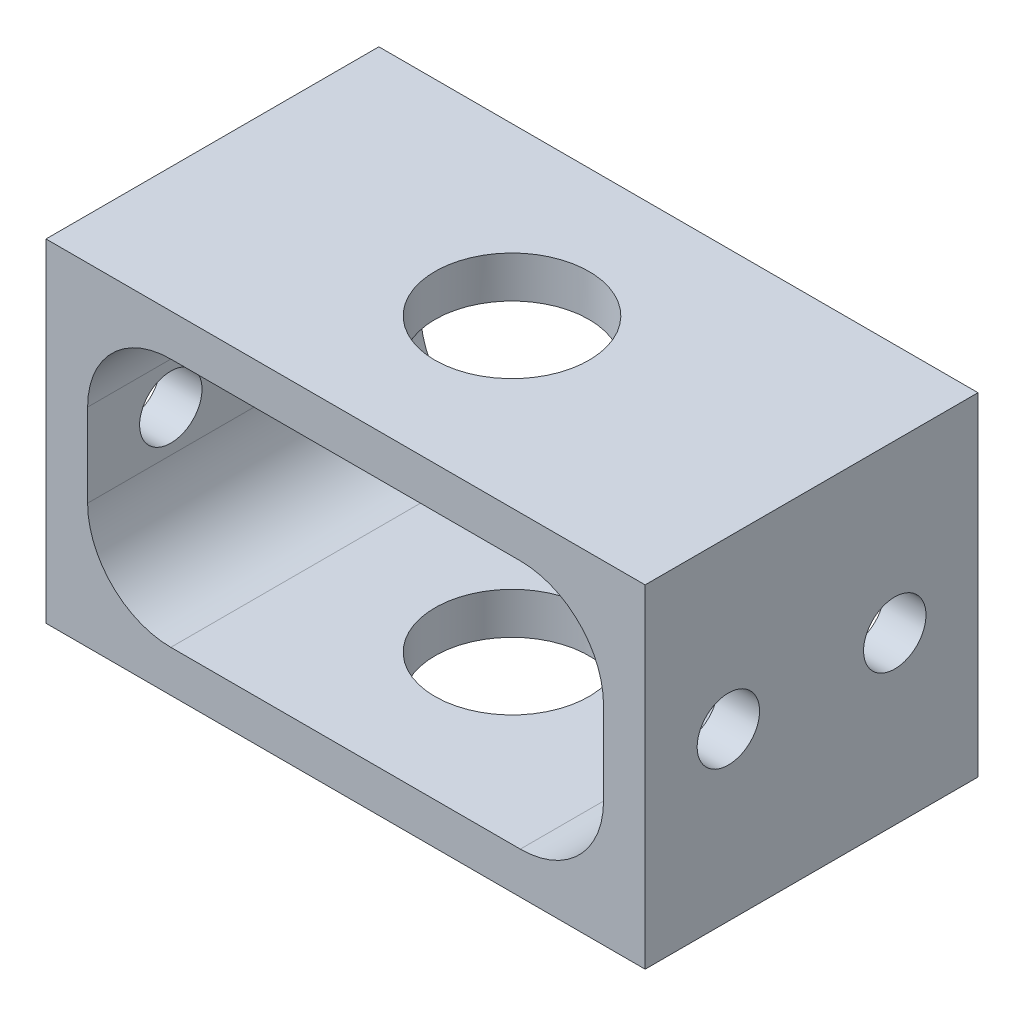
SolidWorks part; units mm, degrees
ref_plane "前视基准面" through (0, 0, 0) normal (0, 0, 1) x (1, 0, 0)
ref_plane "上视基准面" through (0, 0, 0) normal (0, 1, 0) x (1, 0, 0)
ref_plane "右视基准面" through (0, 0, 0) normal (1, 0, 0) x (0, 0, -1)
sketch "草图1" plane through (0, 0, 0) normal (0, 0, 1) x (1, 0, 0)
  line L9 (-14.4, 8) -> (-14.4, -8)
  line L10 (-12.4, 6) -> (12.4, 6)
  line L11 (-12.4, 6) -> (-12.4, -6)
  line L12 (-12.4, -6) -> (12.4, -6)
  line L13 (12.4, 6) -> (12.4, -6)
  line L14 (-12.4, 6) -> (12.4, -6) construction
  line L15 (-12.4, -6) -> (12.4, 6) construction
  line L16 (-14.4, -8) -> (14.4, -8)
  line L17 (14.4, 8) -> (14.4, -8)
  line L18 (-14.4, 8) -> (14.4, 8)
  point P0 (0, 0)
  dimension "D2" = 28.8
  dimension "D3" = 16
  dimension "D1" = 2
extrude "凸台-拉伸1" add sketch "草图1" along normal blind 16
sketch "草图2" plane through (14.4, 0, 0) normal (1, 0, 0) x (0, 0, -1)
  line L0 (-16, -8) -> (-16, 8) construction
  line L1 (0, -8) -> (0, 8) construction
  circle A0 centre (-12, 0) radius 1.5
  circle A1 centre (-4, 0) radius 1.5
  dimension "D1" = 3
  dimension "D2" = 4
  dimension "D3" = 4
extrude "切除-拉伸1" cut sketch "草图2" against normal up to surface (28.8 mm away) up to face at (-14.4, 0, 8)
sketch "草图3" plane through (0, 8, 0) normal (0, 1, 0) x (1, 0, 0)
  circle A0 centre (0, -8) radius 3.7
  dimension "D1" = 7.4
extrude "切除-拉伸2" cut sketch "草图3" against normal up to surface (16 mm away) up to face at (0, -8, 8)
fillet "圆角1" radius 4 4 edges at (12.4, 6, 8) (-12.4, 6, 8) (12.4, -6, 8) (-12.4, -6, 8)
